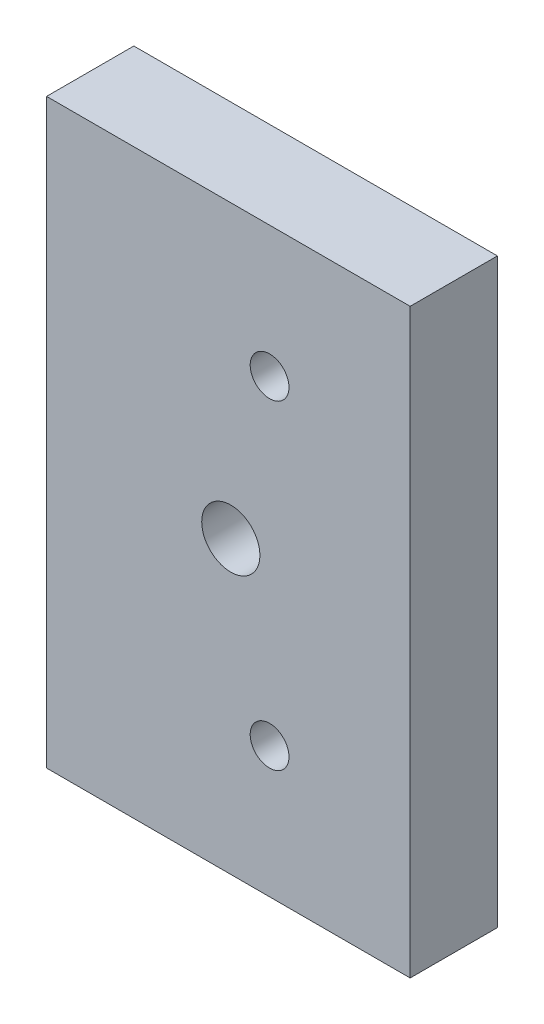
SolidWorks part; units mm, degrees
material "Balsa"
ref_plane "Front Plane" through (0, 0, 0) normal (0, 0, 1) x (1, 0, 0)
ref_plane "Top Plane" through (0, 0, 0) normal (0, 1, 0) x (1, 0, 0)
ref_plane "Right Plane" through (0, 0, 0) normal (1, 0, 0) x (0, 0, -1)
sketch "Sketch1" plane through (0, 0, 0) normal (0, 0, 1) x (1, 0, 0)
  line L1 (-37.5, 60) -> (37.5, 60)
  line L2 (-37.5, 60) -> (-37.5, -60)
  line L3 (-37.5, -60) -> (37.5, -60)
  line L4 (37.5, 60) -> (37.5, -60)
  line L5 (-37.5, 60) -> (37.5, -60) construction
  line L6 (-37.5, -60) -> (37.5, 60) construction
  circle A0 centre (8.5, 33) radius 4
  circle A1 centre (8.5, -33) radius 4
  point P0 (0, 0)
  dimension "D3" = 8
  dimension "D4" = 8
  dimension "D5" = 29
  dimension "D1" = 75
  dimension "D2" = 120
  dimension "D6" = 29
  dimension "D7" = 27
  dimension "D8" = 27
extrude "Boss-Extrude1" add sketch "Sketch1" along normal blind 18
hole_wizard "Ø1.0mm Dowel Hole1" positions "Sketch2" profile "Sketch3" hole size "Ø1.0" standard "ANSI Metric" end condition through all
sketch "Sketch2" plane through (0, 0, 0) normal (0, 0, -1) x (-1, 0, 0)
  line L0 (37.5, 60) -> (37.5, -60) construction
  line L1 (-37.5, 60) -> (37.5, 60) construction
  point P0 (-0.5, 0)
  dimension "D1" = 38
  dimension "D2" = 60
sketch "Sketch3" plane through (0.5, 0, 0) normal (1, 0, 0) x (0, 1, 0)
  line L0 (0, 0) -> (0, 18)
  line L1 (0, 18) -> (6, 18)
  line L2 (6, 18) -> (6, 0)
  line L5 (6, 0) -> (0, 0)
  line L11 (0, -6.35) -> (0, 107.95) construction
  dimension "Thru Hole Dia." = 12
  dimension "Thru Hole Depth" = 18
